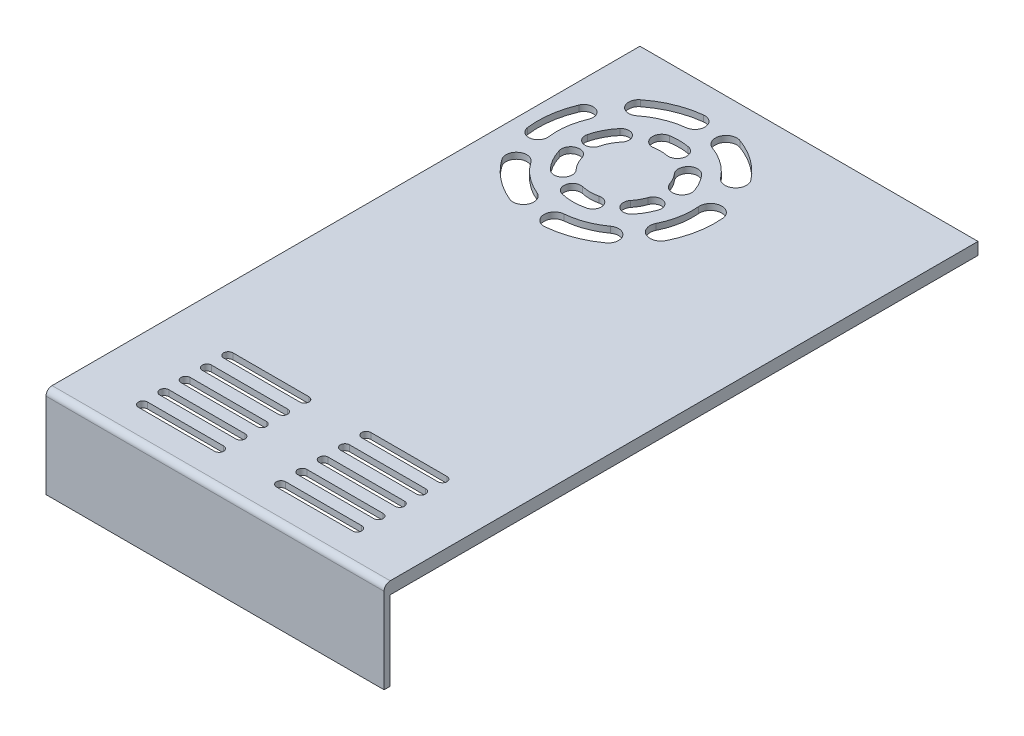
SolidWorks part; units mm, degrees
ref_plane "Front Plane" through (0, 0, 0) normal (0, 0, 1) x (1, 0, 0)
ref_plane "Top Plane" through (0, 0, 0) normal (0, 1, 0) x (1, 0, 0)
ref_plane "Right Plane" through (0, 0, 0) normal (1, 0, 0) x (0, 0, -1)
sketch "Sketch1" plane through (0, 0, 0) normal (0, 1, 0) x (1, 0, 0)
  line L0 (0, 0) -> (111, 0)
  line L1 (111, 0) -> (111, 195)
  line L2 (111, 195) -> (0, 195)
  line L3 (0, 195) -> (0, 0)
  dimension "D1" = 111
  dimension "D2" = 195
extrude "Boss-Extrude3" add sketch "Sketch1" along normal blind 30
sketch "Sketch12" plane through (0, 0, 0) normal (0, -1, 0) x (1, 0, 0)
  line L0 (2, -2) -> (109, -2)
  line L1 (109, -2) -> (109, -193)
  line L2 (109, -193) -> (2, -193)
  line L3 (2, -193) -> (2, -2)
  line L4 (0, -195) -> (0, 0) construction
  line L5 (111, 0) -> (111, -195) construction
  line L6 (111, -195) -> (0, -195) construction
  line L7 (0, 0) -> (111, 0) construction
  dimension "D1" = 2
  dimension "D2" = 2
  dimension "D3" = 2
  dimension "D4" = 2
extrude "Cut-Extrude14" cut sketch "Sketch12" against normal blind 28
sketch "Sketch13" plane through (111, 0, 0) normal (1, 0, 0) x (0, 0, -1)
  line L0 (2, 0) -> (2, 26)
  line L1 (2, 26) -> (195, 26)
  line L2 (195, 30) -> (195, 0) construction
  line L3 (195, 26) -> (195, 0)
  line L4 (195, 0) -> (2, 0)
  line L5 (0, 30) -> (0, 0) construction
  line L6 (0, 30) -> (195, 30) construction
  point P2 (2, 13)
  dimension "D1" = 2
  dimension "D2" = 4
extrude "Cut-Extrude15" cut sketch "Sketch13" against normal through all
sketch "Sketch14" plane through (0, 30, 0) normal (0, 1, 0) x (1, 0, 0)
  line L0 (20.333, 10) -> (45.333, 10)
  line L1 (0, 0) -> (111, 0) construction
  line L4 (65.663, 10) -> (90.663, 10)
  line L10 (20.333, 13) -> (45.333, 13)
  line L12 (45.333, 17) -> (20.333, 17)
  line L14 (20.333, 20) -> (45.333, 20)
  line L16 (20.333, 24) -> (45.333, 24)
  line L18 (45.333, 27) -> (20.333, 27)
  line L20 (45.333, 31) -> (20.333, 31)
  line L22 (20.333, 34) -> (45.333, 34)
  line L24 (45.333, 38) -> (20.333, 38)
  line L26 (20.333, 41) -> (45.333, 41)
  line L28 (90.663, 13) -> (65.663, 13)
  line L30 (65.663, 17) -> (90.663, 17)
  line L32 (90.663, 20) -> (65.663, 20)
  line L34 (65.663, 24) -> (90.663, 24)
  line L36 (90.663, 27) -> (65.663, 27)
  line L38 (65.663, 31) -> (90.663, 31)
  line L40 (90.663, 34) -> (65.663, 34)
  line L42 (65.663, 38) -> (90.663, 38)
  line L44 (90.663, 41) -> (65.663, 41)
  arc A0 (20.333, 41) -> (20.333, 38) centre (20.333, 39.5) ccw
  arc A1 (20.333, 34) -> (20.333, 31) centre (20.333, 32.5) ccw
  arc A2 (20.333, 27) -> (20.333, 24) centre (20.333, 25.5) ccw
  arc A3 (20.333, 20) -> (20.333, 17) centre (20.333, 18.5) ccw
  arc A4 (20.333, 13) -> (20.333, 10) centre (20.333, 11.5) ccw
  arc A5 (45.333, 10) -> (45.333, 13) centre (45.333, 11.5) ccw
  arc A6 (45.333, 17) -> (45.333, 20) centre (45.333, 18.5) ccw
  arc A9 (45.333, 41) -> (45.333, 38) centre (45.333, 39.5) cw
  arc A10 (45.333, 24) -> (45.333, 27) centre (45.333, 25.5) ccw
  arc A11 (45.333, 31) -> (45.333, 34) centre (45.333, 32.5) ccw
  arc A12 (65.663, 41) -> (65.663, 38) centre (65.663, 39.5) ccw
  arc A13 (65.663, 34) -> (65.663, 31) centre (65.663, 32.5) ccw
  arc A14 (65.663, 27) -> (65.663, 24) centre (65.663, 25.5) ccw
  arc A15 (65.663, 20) -> (65.663, 17) centre (65.663, 18.5) ccw
  arc A16 (65.663, 13) -> (65.663, 10) centre (65.663, 11.5) ccw
  arc A17 (90.663, 10) -> (90.663, 13) centre (90.663, 11.5) ccw
  arc A18 (90.663, 17) -> (90.663, 20) centre (90.663, 18.5) ccw
  arc A19 (90.663, 24) -> (90.663, 27) centre (90.663, 25.5) ccw
  arc A20 (90.663, 31) -> (90.663, 34) centre (90.663, 32.5) ccw
  arc A21 (90.663, 38) -> (90.663, 41) centre (90.663, 39.5) ccw
  point P17 (78.163, 34)
  dimension "D2" = 10
  dimension "D3" = 3
  dimension "D4" = 4
  dimension "D5" = 3
  dimension "D10" = 4
extrude "Cut-Extrude18" cut sketch "Sketch14" against normal blind 28
sketch "Sketch15" plane through (0, 30, 0) normal (0, 1, 0) x (1, 0, 0)
  arc A1 (9.517, 167.06) -> (7.7109, 153.851) centre (33.2444, 157.0876) ccw construction
  arc A2 (6.6963, 168.2455) -> (4.6754, 153.4662) centre (33.2444, 157.0876) ccw
  arc A3 (12.3378, 165.8745) -> (10.7463, 154.2358) centre (33.2444, 157.0876) ccw
  arc A4 (12.3378, 165.8745) -> (6.6963, 168.2455) centre (9.517, 167.06) ccw
  arc A5 (4.6754, 153.4662) -> (10.7463, 154.2358) centre (7.7109, 153.851) ccw
  arc A6 (17.2961, 177.2888) -> (30.4021, 182.668) centre (33.2444, 157.0876) cw construction
  arc A7 (30.0424, 185.9056) -> (15.2776, 179.8456) centre (33.2444, 157.0876) ccw
  arc A8 (30.7618, 179.4304) -> (19.3146, 174.732) centre (33.2444, 157.0876) ccw
  arc A9 (30.7618, 179.4304) -> (30.0424, 185.9056) centre (30.4021, 182.668) ccw
  arc A10 (15.2776, 179.8456) -> (19.3146, 174.732) centre (17.2961, 177.2888) ccw
  arc A11 (42.0119, 181.2861) -> (53.5208, 172.9401) centre (33.2444, 157.0876) cw construction
  arc A16 (12.2767, 142.1615) -> (23.4717, 133.2773) centre (33.2444, 157.0876) ccw construction
  arc A21 (9.4916, 140.1789) -> (22.1736, 130.1147) centre (33.2444, 157.0876) ccw
  arc A26 (15.0617, 144.144) -> (24.7697, 136.4399) centre (33.2444, 157.0876) ccw
  arc A35 (15.0617, 144.144) -> (9.4916, 140.1789) centre (12.2767, 142.1615) ccw
  arc A36 (22.1736, 130.1147) -> (24.7697, 136.4399) centre (23.4717, 133.2773) ccw
  arc A37 (56.3106, 175.1212) -> (43.2182, 184.6155) centre (33.2444, 157.0876) ccw
  arc A38 (50.731, 170.759) -> (40.8056, 177.9567) centre (33.2444, 157.0876) ccw
  arc A39 (50.731, 170.759) -> (56.3106, 175.1212) centre (53.5208, 172.9401) ccw
  arc A40 (43.2182, 184.6155) -> (40.8056, 177.9567) centre (42.0119, 181.2861) ccw
  arc A41 (58.8854, 159.3173) -> (56.3106, 145.669) centre (33.2444, 157.0876) cw construction
  arc A42 (59.5866, 144.0473) -> (62.5271, 159.6339) centre (33.2444, 157.0876) ccw
  arc A43 (53.0346, 147.2908) -> (55.2438, 159.0006) centre (33.2444, 157.0876) ccw
  arc A44 (53.0346, 147.2908) -> (59.5866, 144.0473) centre (56.3106, 145.669) ccw
  arc A45 (62.5271, 159.6339) -> (55.2438, 159.0006) centre (58.8854, 159.3173) ccw
  arc A46 (35.474, 131.4466) -> (48.3541, 136.2518) centre (33.2444, 157.0876) ccw construction
  arc A47 (35.768, 128.0659) -> (50.3462, 133.5047) centre (33.2444, 157.0876) ccw
  arc A48 (35.1801, 134.8272) -> (46.3619, 138.9989) centre (33.2444, 157.0876) ccw
  arc A49 (35.1801, 134.8272) -> (35.768, 128.0659) centre (35.474, 131.4466) ccw
  arc A50 (50.3462, 133.5047) -> (46.3619, 138.9989) centre (48.3541, 136.2518) ccw
  arc A52 (19.1319, 160.5745) -> (22.1875, 166.5251) centre (33.2444, 157.0876) cw construction
  arc A57 (30.7618, 171.4109) -> (35.9299, 171.3743) centre (33.2444, 157.0876) cw construction
  arc A67 (44.4821, 147.8662) -> (46.9759, 152.3162) centre (33.2444, 157.0876) ccw construction
  arc A84 (19.3146, 152.9306) -> (22.5047, 147.2908) centre (33.2444, 157.0876) ccw construction
  arc A85 (16.4417, 152.0732) -> (20.2897, 145.2702) centre (33.2444, 157.0876) ccw
  arc A86 (22.1875, 153.7879) -> (24.7197, 149.3113) centre (33.2444, 157.0876) ccw
  arc A87 (22.1875, 153.7879) -> (16.4417, 152.0732) centre (19.3146, 152.9306) ccw
  arc A88 (20.2897, 145.2702) -> (24.7197, 149.3113) centre (22.5047, 147.2908) ccw
  arc A89 (29.9166, 142.9368) -> (36.5722, 142.9368) centre (33.2444, 157.0876) ccw construction
  arc A90 (29.2744, 140.2057) -> (37.2144, 140.2057) centre (33.2444, 157.0876) ccw
  arc A91 (30.5589, 145.6679) -> (35.9299, 145.6679) centre (33.2444, 157.0876) ccw
  arc A92 (30.5589, 145.6679) -> (29.2744, 140.2057) centre (29.9166, 142.9368) ccw
  arc A93 (37.2144, 140.2057) -> (35.9299, 145.6679) centre (36.5722, 142.9368) ccw
  arc A94 (46.6244, 146.1082) -> (49.5936, 151.4066) centre (33.2444, 157.0876) ccw
  arc A95 (42.3397, 149.6242) -> (44.3581, 153.2258) centre (33.2444, 157.0876) ccw
  arc A96 (42.3397, 149.6242) -> (46.6244, 146.1082) centre (44.4821, 147.8662) ccw
  arc A97 (49.5936, 151.4066) -> (44.3581, 153.2258) centre (46.9759, 152.3162) ccw
  arc A98 (44.3581, 166.4581) -> (46.9759, 161.8591) centre (33.2444, 157.0876) cw construction
  arc A99 (49.9728, 162.9004) -> (46.7837, 168.5032) centre (33.2444, 157.0876) ccw
  arc A100 (43.9789, 160.8177) -> (41.9325, 164.4129) centre (33.2444, 157.0876) ccw
  arc A101 (43.9789, 160.8177) -> (49.9728, 162.9004) centre (46.9759, 161.8591) ccw
  arc A102 (46.7837, 168.5032) -> (41.9325, 164.4129) centre (44.3581, 166.4581) ccw
  arc A107 (20.1117, 168.297) -> (16.4823, 161.2291) centre (33.2444, 157.0876) ccw
  arc A108 (24.2634, 164.7533) -> (21.7815, 159.9198) centre (33.2444, 157.0876) ccw
  arc A109 (24.2634, 164.7533) -> (20.1117, 168.297) centre (22.1875, 166.5251) ccw
  arc A110 (16.4823, 161.2291) -> (21.7815, 159.9198) centre (19.1319, 160.5745) ccw
  arc A111 (36.4923, 174.3663) -> (30.2419, 174.4107) centre (33.2444, 157.0876) ccw
  arc A112 (35.3675, 168.3822) -> (31.2818, 168.4112) centre (33.2444, 157.0876) ccw
  arc A113 (35.3675, 168.3822) -> (36.4923, 174.3663) centre (35.9299, 171.3743) ccw
  arc A114 (30.2419, 174.4107) -> (31.2818, 168.4112) centre (30.7618, 171.4109) ccw
  point P5 (7.7438, 160.5745)
  point P13 (23.4717, 180.8979)
  point P21 (48.3541, 177.9235)
  point P29 (17.2452, 136.9268)
  point P37 (58.5361, 152.3162)
  point P45 (42.2408, 132.9733)
  point P53 (20.3128, 163.7279)
  point P62 (33.3475, 171.6241)
  point P69 (20.5914, 149.9307)
  point P78 (45.9257, 149.981)
  point P85 (33.2444, 142.5508)
  point P93 (45.878, 164.2787)
extrude "Cut-Extrude20" cut sketch "Sketch15" against normal blind 28
fillet "Fillet1" radius 2 1 edges at (55.5, 30, 0)
